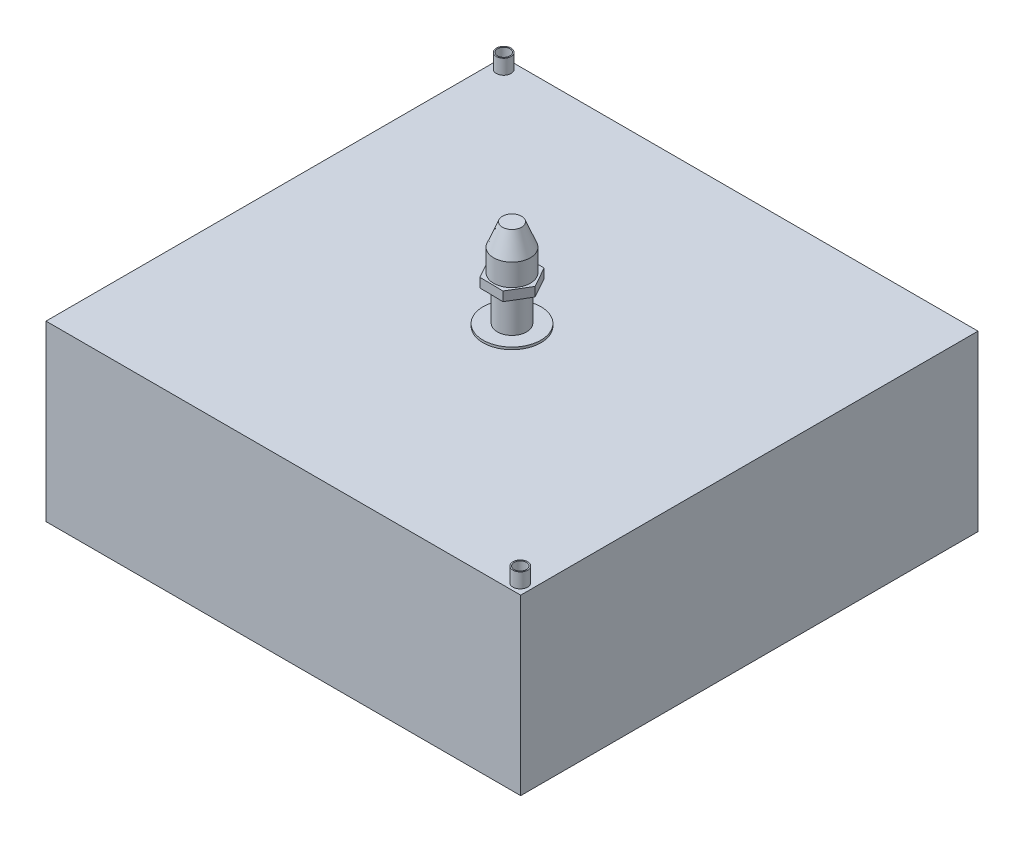
SolidWorks part; units mm, degrees
ref_plane "Front Plane" through (0, 0, 0) normal (0, 0, 1) x (1, 0, 0)
ref_plane "Top Plane" through (0, 0, 0) normal (0, 1, 0) x (1, 0, 0)
ref_plane "Right Plane" through (0, 0, 0) normal (1, 0, 0) x (0, 0, -1)
sketch "Sketch1" plane through (0, 0, 0) normal (0, 0, 1) x (1, 0, 0)
  line L1 (-205, 150) -> (205, 150)
  line L2 (-205, 150) -> (-205, 0)
  line L3 (-205, 0) -> (205, 0)
  line L4 (205, 150) -> (205, 0)
  dimension "D1" = 410
  dimension "D2" = 150
extrude "Extrude1" add sketch "Sketch1" along normal mid plane 395
sketch "Sketch2" plane through (0, 150, 0) normal (0, 1, 0) x (1, 0, 0)
  line L0 (0, 0) -> (-205, 197.5) construction
  line L1 (0, 0) -> (205, -197.5) construction
  line L2 (-195.8476, 197.5) -> (-205, 188.0001) construction
  line L3 (205, 197.5) -> (-205, 197.5) construction
  line L4 (-205, -197.5) -> (-205, 197.5) construction
  line L5 (-195.8476, 197.5) -> (-191.2746, 193.0943) construction
  line L6 (205, -188.0001) -> (195.8476, -197.5) construction
  line L7 (205, -197.5) -> (205, 197.5) construction
  line L8 (205, -197.5) -> (-205, -197.5) construction
  line L9 (191.2746, -193.0943) -> (195.8476, -197.5) construction
  circle A0 centre (-195.6803, 188.5213) radius 6.35
  circle A1 centre (195.6803, -188.5213) radius 6.35
  dimension "D1" = 12.7
extrude "Extrude2" add sketch "Sketch2" along normal blind 12.7
shell "Shell1" thickness 1
sketch "Sketch3" plane through (0, 150, 0) normal (0, 1, 0) x (1, 0, 0)
  circle A0 centre (0, 0) radius 25
  dimension "D1" = 50
extrude "Extrude3" add sketch "Sketch3" along normal blind 2
sketch "Sketch4" plane through (0, 152, 0) normal (0, 1, 0) x (1, 0, 0)
  circle A0 centre (0, 0) radius 12.7
  dimension "D1" = 25.4
extrude "Extrude4" add sketch "Sketch4" along normal blind 30
sketch "Sketch5" plane through (0, 182, 0) normal (0, 1, 0) x (1, 0, 0)
  line L1 (10.3965, 17.3276) -> (-9.8079, 17.6675)
  line L2 (-9.8079, 17.6675) -> (-20.2044, 0.3399)
  line L3 (-20.2044, 0.3399) -> (-10.3965, -17.3276)
  line L4 (-10.3965, -17.3276) -> (9.8079, -17.6675)
  line L5 (9.8079, -17.6675) -> (20.2044, -0.3399)
  line L6 (20.2044, -0.3399) -> (10.3965, 17.3276)
  circle A0 centre (0, 0) radius 17.5 construction
  dimension "D1" = 35
extrude "Extrude5" add sketch "Sketch5" along normal blind 8
sketch "Sketch6" plane through (0, 0, 0) normal (0, 0, 1) x (1, 0, 0)
  line L0 (0, 0) -> (0, 200.8978) construction
  line L1 (0, 190) -> (15.875, 190)
  line L2 (15.875, 190) -> (15.875, 209.05)
  line L3 (8.255, 228.1) -> (0, 228.1)
  line L4 (0, 228.1) -> (0, 190)
  line L5 (15.875, 209.05) -> (8.255, 228.1)
  line L6 (-10.3965, 190) -> (9.8079, 190) construction
  dimension "D1" = 31.75
  dimension "D2" = 38.1
  dimension "D3" = 8.255
  dimension "D4" = 19.05
revolve "Revolve1" add sketch "Sketch6" angle 360 about L0
